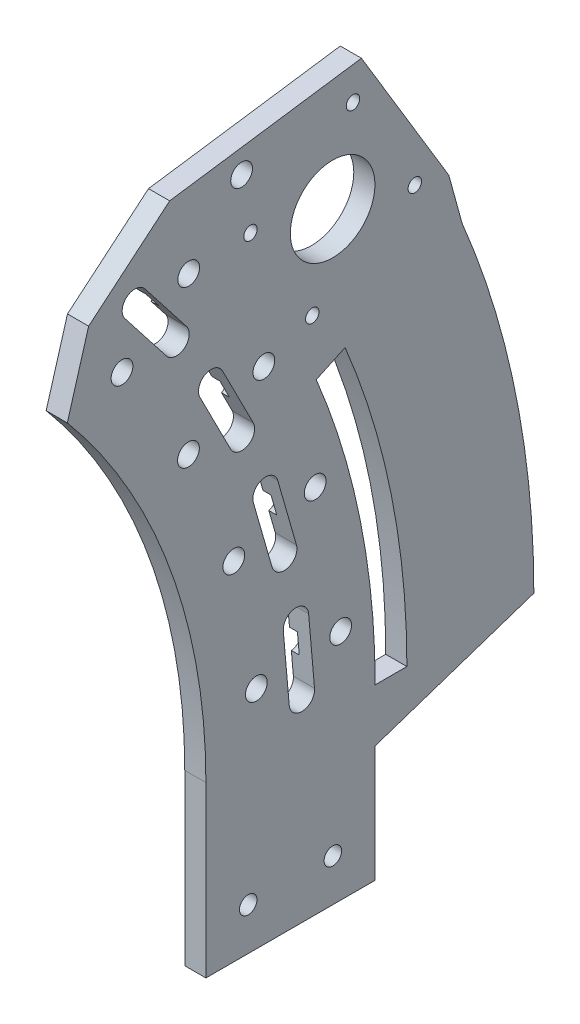
SolidWorks part; units mm, degrees
other "Markup1"
sketch "Sketch5" plane through (7.4724, -50.8, -116.7452) normal (0.7166, -0.0822, 0.6926) x (0.6913, -0.0479, -0.721)
other "Markup2"
sketch "Sketch6" plane through (7.4724, -50.8, -116.7452) normal (0.7166, -0.0822, 0.6926) x (0.6913, -0.0479, -0.721)
material "6061-T6 (SS)"
ref_plane "Front Plane" through (0, 0, 0) normal (0, 0, 1) x (1, 0, 0)
ref_plane "Top Plane" through (0, 0, 0) normal (0, 1, 0) x (1, 0, 0)
ref_plane "Right Plane" through (0, 0, 0) normal (1, 0, 0) x (0, 0, -1)
sketch "Sketch1" plane through (0, 0, 0) normal (1, 0, 0) x (0, 0, -1)
  line L0 (0, 0) -> (177.8, 0) construction
  line L1 (0, 0) -> (136.2027, 114.2876) construction
  line L2 (177.8, 0) -> (177.8, -50.8)
  line L3 (177.8, -50.8) -> (228.6, -50.8)
  line L4 (228.6, -50.8) -> (228.6, 0) construction
  line L5 (136.2027, 114.2876) -> (148.2956, 124.4347) construction
  line L6 (177.8, 0) -> (228.6, 0) construction
  line L7 (136.2027, 114.2876) -> (148.2956, 124.4347) construction
  line L8 (0, 0) -> (202.4268, 17.71) construction
  line L9 (0, 0) -> (0, 168.3639) construction
  line L10 (202.4268, 17.71) -> (208.7526, 18.2635) construction
  line L11 (0, 0) -> (200.1129, 35.2853) construction
  line L12 (0, 0) -> (196.2761, 52.592) construction
  line L13 (0, 0) -> (190.9455, 69.4985) construction
  line L14 (0, 0) -> (184.1617, 85.876) construction
  line L15 (0, 0) -> (175.9764, 101.6) construction
  line L16 (0, 0) -> (166.4517, 116.5507) construction
  line L17 (0, 0) -> (200.1129, 35.2853) construction
  line L18 (0, 0) -> (196.2761, 52.592) construction
  line L19 (208.7526, 18.2635) -> (221.4043, 19.3704) construction
  line L20 (206.3665, 36.388) -> (218.8735, 38.5933) construction
  line L21 (202.4098, 54.2355) -> (214.677, 57.5225) construction
  line L22 (196.9126, 71.6703) -> (208.8467, 76.014) construction
  line L23 (189.9168, 88.5597) -> (201.4269, 93.9269) construction
  line L24 (181.4756, 104.775) -> (192.4741, 111.125) construction
  line L25 (171.6533, 120.1929) -> (182.0565, 127.4774) construction
  line L26 (0, 0) -> (208.7526, 18.2635) construction
  line L27 (0, 0) -> (206.3665, 36.388) construction
  line L28 (177.8, -50.8) -> (177.8, -38.1) construction
  line L29 (177.8, -38.1) -> (228.6, -38.1) construction
  line L30 (0, 0) -> (42824.6192, 25807.9831) construction
  line L31 (215.8361, 130.0722) -> (202.7256, 151.8271) construction
  line L32 (215.8361, 130.0722) -> (228.9465, 108.3173) construction
  line L33 (237.591, 143.1827) -> (224.4805, 164.9376)
  line L34 (237.591, 143.1827) -> (250.7014, 121.4278)
  line L36 (197.1944, 161.0054) -> (224.4805, 164.9376)
  line L37 (219.5586, 92.1822) -> (234.4777, 99.1391) construction
  line L38 (210.9192, 88.1536) -> (234.4777, 99.1391) construction
  line L39 (234.4777, 99.1391) -> (250.7014, 121.4278) construction
  line L40 (219.5586, 92.1822) -> (210.9192, 88.1536)
  line L41 (228.6, 0) -> (238.125, 0)
  line L42 (228.6, -15.875) -> (276.225, 0)
  line L43 (250.7014, 121.4278) -> (254.6879, 106.9313)
  line L44 (228.6, -50.8) -> (228.6, -15.875)
  line L45 (215.8361, 130.0722) -> (211.2933, 111.7501) construction
  line L47 (0, 0) -> (136.2027, 114.2876) construction
  line L48 (136.2027, 114.2876) -> (142.6, 136.2343)
  line L49 (142.6, 136.2343) -> (166.9219, 156.6428)
  line L50 (166.9219, 156.6428) -> (197.1944, 161.0054)
  line L51 (209.7235, 105.4187) -> (215.8361, 130.0722) construction
  line L52 (215.8361, 130.0722) -> (221.9486, 154.7258) construction
  arc A0 (177.8, 0) -> (136.2027, 114.2876) centre (0, 0) ccw
  arc A1 (228.6, 0) -> (210.9192, 88.1536) centre (0, 0) ccw
  circle A2 centre (202.4268, 17.71) radius 6.35 construction
  arc A4 (208.7526, 18.2635) -> (160.5246, 134.6961) centre (0, 0) ccw construction
  arc A5 (215.0784, 18.8169) -> (165.389, 138.7778) centre (0, 0) ccw construction
  circle A7 centre (221.4043, 19.3704) radius 6.35 construction
  circle A9 centre (200.1129, 35.2853) radius 6.35 construction
  circle A11 centre (196.2761, 52.592) radius 6.35 construction
  circle A13 centre (190.9455, 69.4985) radius 6.35 construction
  circle A15 centre (184.1617, 85.876) radius 6.35 construction
  circle A17 centre (175.9764, 101.6) radius 6.35 construction
  circle A19 centre (166.4517, 116.5507) radius 6.35 construction
  circle A21 centre (218.8735, 38.5933) radius 6.35 construction
  circle A23 centre (214.677, 57.5225) radius 6.35 construction
  circle A25 centre (208.8467, 76.014) radius 6.35 construction
  circle A27 centre (201.4269, 93.9269) radius 6.35 construction
  circle A29 centre (192.4741, 111.125) radius 6.35 construction
  circle A31 centre (182.0565, 127.4774) radius 6.35 construction
  circle A32 centre (190.5, -38.1) radius 2.6289
  circle A33 centre (215.9, -38.1) radius 2.6289
  circle A34 centre (215.8361, 130.0722) radius 12.7
  circle A36 centre (228.9465, 108.3173) radius 2.0193 construction
  arc A37 (219.5586, 92.1822) -> (238.125, 0) centre (0, 0) cw
  arc A38 (254.6879, 106.9313) -> (276.225, 0) centre (0, 0) cw
  circle A41 centre (191.1825, 136.1848) radius 2.0193
  circle A42 centre (221.9486, 154.7258) radius 2.0193
  circle A45 centre (215.8361, 130.0722) radius 12.7
  circle A46 centre (240.4896, 123.9597) radius 2.0193
  circle A47 centre (215.8361, 130.0722) radius 12.7
  circle A48 centre (209.7235, 105.4187) radius 2.0193
  circle A49 centre (215.8361, 130.0722) radius 12.7
  point P11 (177.1234, 15.4963)
  point P24 (175.0988, 30.8746)
  point P82 (237.591, 143.1827)
  point P124 (215.8361, 130.0722)
  dimension "D5" = 12.7
  dimension "D7" = 22.86
  dimension "D12" = 12.7
  dimension "D24" = 5.2578
  dimension "D25" = 5.2578
  dimension "D28" = 25.4
  dimension "D30" = 25.4
  dimension "D32" = 4.0386
  dimension "D35" = 9.525
  dimension "D43" = 4.0386
  dimension "D1" = 177.8
  dimension "D2" = 40
  dimension "D3" = 50.8
  dimension "D4" = 50.8
  dimension "D6" = 5
  dimension "D8" = 25.4
  dimension "D10" = 90
  dimension "D13" = 25.4
  dimension "D14" = 5
  dimension "D16" = 5
  dimension "D17" = 6.35
  dimension "D20" = 5
  dimension "D21" = 12.7
  dimension "D22" = 12.7
  dimension "D23" = 12.7
  dimension "D26" = 8.925
  dimension "D27" = 252
  dimension "D29" = 25.4
  dimension "D31" = 25.4
  dimension "D33" = 25.4
  dimension "D34" = 25.4
  dimension "D37" = 15.875
  dimension "D38" = 45
  dimension "D41" = 12.7
  dimension "D42" = 31.75
  dimension "D9" = 6.35
  dimension "D36" = 38.1
  dimension "D15" = 6
  dimension "D19" = 7
  dimension "D45" = 4
extrude "Boss-Extrude1" add sketch "Sketch1" along normal blind 6.35
sketch "Sketch7" plane through (0, 0, 0) normal (0, 0, 1) x (1, 0, 0)
  line L0 (0, 0) -> (50000, 0) construction
sketch "Sketch8" plane through (0, 0, 0) normal (-1, 0, 0) x (0, 0, 1)
  line L0 (0, 0) -> (-218.2414, 19.0936) construction
  line L1 (0, 0) -> (-81.6847, 0) construction
  line L2 (0, 0) -> (-210.5884, 60.3853) construction
  line L3 (0, 0) -> (-195.1973, 99.458) construction
  line L4 (0, 0) -> (-172.6335, 134.876) construction
  line L5 (-201.0352, 27.7871) -> (-202.8062, 7.5444)
  line L6 (-192.0396, 65.6359) -> (-197.6405, 46.1031)
  line L7 (0, 0) -> (-192.938, 16.8799) construction
  line L8 (0, 0) -> (-186.1724, 53.3841) construction
  line L9 (-202.8062, 7.5444) -> (-201.0352, 27.7871) construction
  line L10 (-201.0352, 27.7871) -> (-208.6262, 28.4512) construction
  line L11 (-208.6262, 28.4512) -> (-210.3972, 8.2086)
  line L12 (-210.3972, 8.2086) -> (-202.8062, 7.5444) construction
  line L13 (-204.9653, 48.2034) -> (-197.6405, 46.1031) construction
  line L15 (-192.0396, 65.6359) -> (-199.3644, 67.7363) construction
  line L16 (-199.3644, 67.7363) -> (-204.9653, 48.2034)
  line L17 (-192.0019, 86.427) -> (-185.2124, 82.9676) construction
  line L19 (-175.9874, 101.0729) -> (-182.7768, 104.5323) construction
  line L20 (-182.7768, 104.5323) -> (-192.0019, 86.427)
  line L21 (-171.9832, 121.4748) -> (-165.9786, 116.7835) construction
  line L23 (-153.4684, 132.7958) -> (-159.473, 137.4872) construction
  line L24 (-159.473, 137.4872) -> (-171.9832, 121.4748)
  line L25 (-197.6405, 46.1031) -> (-192.0396, 65.6359) [skipped]
  line L27 (-185.2124, 82.9676) -> (-175.9874, 101.0729) [skipped]
  line L28 (-175.9874, 101.0729) -> (-185.2124, 82.9676)
  line L30 (-165.9786, 116.7835) -> (-153.4684, 132.7958) [skipped]
  line L34 (-165.9786, 116.7835) -> (-153.4684, 132.7958)
  circle A0 centre (-218.2414, 19.0936) radius 3.2639
  arc A1 (-208.6262, 28.4512) -> (-201.0352, 27.7871) centre (-204.8307, 28.1192) cw
  circle A2 centre (-192.938, 16.8799) radius 3.2639
  circle A3 centre (-210.5884, 60.3853) radius 3.2639
  circle A4 centre (-186.1724, 53.3841) radius 3.2639
  circle A5 centre (-195.1973, 99.458) radius 3.2639
  circle A6 centre (-172.5657, 87.9266) radius 3.2639
  circle A7 centre (-172.6335, 134.876) radius 3.2639
  circle A8 centre (-152.618, 119.2382) radius 3.2639
  arc A13 (-210.3972, 8.2086) -> (-202.8062, 7.5444) centre (-206.6017, 7.8765) ccw
  arc A14 (-204.9653, 48.2034) -> (-197.6405, 46.1031) centre (-201.3029, 47.1532) ccw
  arc A15 (-199.3644, 67.7363) -> (-192.0396, 65.6359) centre (-195.702, 66.6861) cw
  arc A16 (-192.0019, 86.427) -> (-185.2124, 82.9676) centre (-188.6072, 84.6973) ccw
  arc A17 (-182.7768, 104.5323) -> (-175.9874, 101.0729) centre (-179.3821, 102.8026) cw
  arc A18 (-159.473, 137.4872) -> (-153.4684, 132.7958) centre (-156.4707, 135.1415) cw
  arc A19 (-171.9832, 121.4748) -> (-165.9786, 116.7835) centre (-168.9809, 119.1291) ccw
  dimension "D3" = 6.5278
  dimension "D4" = 6.5278
  dimension "D1" = 219.075
  dimension "D2" = 5
  dimension "D5" = 25.4
  dimension "D7" = 11
  dimension "D8" = 20.32
  dimension "D9" = 7.62
  dimension "D10" = 10.16
  dimension "D11" = 9.017
  dimension "D6" = 4
extrude "Cut-Extrude1" cut sketch "Sketch8" against normal through all
sketch "Sketch9" plane through (0, 18.3299, -209.5117) normal (-1, 0, 0) x (0, -0.0872, 0.9962)
  line L0 (0, 0) -> (-2.3812, 0) construction
  line L1 (0, 10.16) -> (0, -10.16) construction
  line L3 (7.62, -10.16) -> (7.62, 10.16) construction
  circle A1 centre (0, 0) radius 3.175
  circle A2 centre (7.62, 0) radius 3.175
  dimension "D1" = 6.35
  dimension "D3" = 6.35
  dimension "D2" = 2.3812
extrude "Cut-Extrude2" cut sketch "Sketch9" against normal blind 2.3813 and the other way blind 10.033
pattern_circular "CirPattern1" count 4 every 11 about axis through (0, 0, 0) along (1, 0, 0) of "Cut-Extrude2"
sketch "Sketch10" plane through (0, 0, 0) normal (-1, 0, 0) x (0, 0, 1)
  line L0 (0, 0) -> (-188.5123, 152.6542) construction
  line L1 (0, 0) -> (-65.3997, 0) construction
  circle A0 centre (-188.5123, 152.6542) radius 3.2639
  dimension "D1" = 6.5278
  dimension "D2" = 242.57
  dimension "D3" = 39
extrude "Cut-Extrude3" cut sketch "Sketch10" against normal through all
